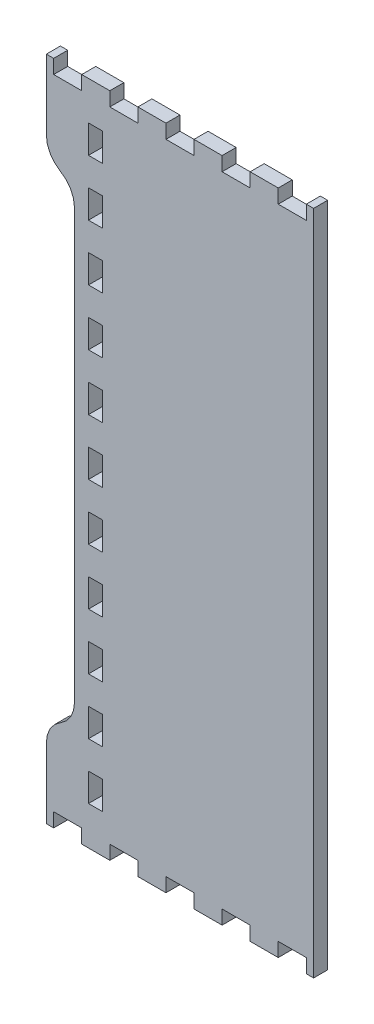
SolidWorks part; units mm, degrees
ref_plane "Front Plane" through (0, 0, 0) normal (0, 0, 1) x (1, 0, 0)
ref_plane "Top Plane" through (0, 0, 0) normal (0, 1, 0) x (1, 0, 0)
ref_plane "Right Plane" through (0, 0, 0) normal (1, 0, 0) x (0, 0, -1)
sketch "Model" plane through (0, 0, 0) normal (0, 0, 1) x (1, 0, 0)
  line L558 (863.264, 22.8602) -> (866.2368, 22.8602)
  line L559 (866.2368, 22.8602) -> (866.2368, 28.5752)
  line L560 (866.2368, 28.5752) -> (877.6675, 28.5752)
  line L561 (877.6675, 28.5752) -> (877.6675, 22.8602)
  line L562 (877.6675, 22.8602) -> (889.0983, 22.8602)
  line L563 (889.0983, 22.8602) -> (889.0983, 28.5752)
  line L564 (889.0983, 28.5752) -> (900.529, 28.5752)
  line L565 (900.529, 28.5752) -> (900.529, 22.8602)
  line L566 (900.529, 22.8602) -> (911.9562, 22.8602)
  line L567 (911.9562, 22.8602) -> (911.9562, 28.5752)
  line L568 (911.9562, 28.5752) -> (923.3869, 28.5752)
  line L569 (923.3869, 28.5752) -> (923.3869, 22.8602)
  line L570 (923.3869, 22.8602) -> (934.8176, 22.8602)
  line L571 (934.8176, 22.8602) -> (934.8176, 28.5752)
  line L572 (934.8176, 28.5752) -> (946.2483, 28.5752)
  line L573 (946.2483, 28.5752) -> (946.2483, 22.8602)
  line L574 (946.2483, 22.8602) -> (957.679, 22.8602)
  line L575 (957.679, 22.8602) -> (957.679, 28.5752)
  line L576 (957.679, 28.5752) -> (969.1062, 28.5752)
  line L577 (969.1062, 28.5752) -> (969.1062, 22.8602)
  line L578 (969.1062, 22.8602) -> (972.0826, 22.8602)
  line L579 (972.0826, 22.8602) -> (972.0826, 28.5752)
  line L580 (972.0826, 28.5752) -> (972.0826, 288.5754)
  line L581 (972.0826, 288.5754) -> (972.0826, 294.2904)
  line L582 (972.0826, 294.2904) -> (969.1062, 294.2904)
  line L583 (969.1062, 294.2904) -> (969.1062, 288.5754)
  line L584 (969.1062, 288.5754) -> (957.679, 288.5754)
  line L585 (957.679, 288.5754) -> (957.679, 294.2904)
  line L586 (957.679, 294.2904) -> (946.2483, 294.2904)
  line L587 (946.2483, 294.2904) -> (946.2483, 288.5754)
  line L588 (946.2483, 288.5754) -> (934.8176, 288.5754)
  line L589 (934.8176, 288.5754) -> (934.8176, 294.2904)
  line L590 (934.8176, 294.2904) -> (923.3869, 294.2904)
  line L591 (923.3869, 294.2904) -> (923.3869, 288.5754)
  line L592 (923.3869, 288.5754) -> (911.9562, 288.5754)
  line L593 (911.9562, 288.5754) -> (911.9562, 294.2904)
  line L594 (911.9562, 294.2904) -> (900.529, 294.2904)
  line L595 (900.529, 294.2904) -> (900.529, 288.5754)
  line L596 (900.529, 288.5754) -> (889.0983, 288.5754)
  line L597 (889.0983, 288.5754) -> (889.0983, 294.2904)
  line L598 (889.0983, 294.2904) -> (877.6675, 294.2904)
  line L599 (877.6675, 294.2904) -> (877.6675, 288.5754)
  line L600 (877.6675, 288.5754) -> (866.2368, 288.5754)
  line L601 (866.2368, 288.5754) -> (866.2368, 294.2904)
  line L602 (866.2368, 294.2904) -> (863.264, 294.2904)
  line L603 (863.264, 294.2904) -> (863.264, 288.5754)
  line L604 (863.264, 288.5754) -> (863.264, 265.7154)
  line L605 (863.264, 265.7154) -> (863.6533, 262.7573)
  line L606 (863.6533, 262.7573) -> (864.7947, 260.0004)
  line L607 (864.7947, 260.0004) -> (866.6102, 257.6331)
  line L608 (866.6102, 257.6331) -> (868.9758, 255.8164)
  line L609 (868.9758, 255.8164) -> (871.3445, 254.0001)
  line L610 (871.3445, 254.0001) -> (873.1604, 251.6332)
  line L611 (873.1604, 251.6332) -> (874.3036, 248.8763)
  line L612 (874.3036, 248.8763) -> (874.6947, 245.9182)
  line L613 (874.6947, 245.9182) -> (874.6947, 71.2322)
  line L614 (874.6947, 71.2322) -> (874.3023, 68.2743)
  line L615 (874.3023, 68.2743) -> (873.1604, 65.5172)
  line L616 (873.1604, 65.5172) -> (871.3445, 63.1505)
  line L617 (871.3445, 63.1505) -> (868.9758, 61.3344)
  line L618 (868.9758, 61.3344) -> (866.6102, 59.5176)
  line L619 (866.6102, 59.5176) -> (864.7947, 57.1504)
  line L620 (864.7947, 57.1504) -> (863.6533, 54.3934)
  line L621 (863.6533, 54.3934) -> (863.264, 51.4354)
  line L622 (863.264, 51.4354) -> (863.264, 28.5752)
  line L623 (863.264, 28.5752) -> (863.264, 22.8602)
  line L624 (880.4101, 272.8754) -> (880.4101, 278.5904)
  line L625 (880.4101, 278.5904) -> (886.1219, 278.5904)
  line L626 (886.1219, 278.5904) -> (886.1219, 267.1603)
  line L627 (886.1219, 267.1603) -> (880.4101, 267.1603)
  line L628 (880.4101, 267.1603) -> (880.4101, 272.8754)
  line L629 (880.4101, 250.0153) -> (880.4101, 255.7303)
  line L630 (880.4101, 255.7303) -> (886.1219, 255.7303)
  line L631 (886.1219, 255.7303) -> (886.1219, 244.3003)
  line L632 (886.1219, 244.3003) -> (880.4101, 244.3003)
  line L633 (880.4101, 244.3003) -> (880.4101, 250.0153)
  line L634 (880.4101, 227.1553) -> (880.4101, 232.8703)
  line L635 (880.4101, 232.8703) -> (886.1219, 232.8703)
  line L636 (886.1219, 232.8703) -> (886.1219, 221.4403)
  line L637 (886.1219, 221.4403) -> (880.4101, 221.4403)
  line L638 (880.4101, 221.4403) -> (880.4101, 227.1553)
  line L639 (880.4101, 204.2953) -> (880.4101, 210.0103)
  line L640 (880.4101, 210.0103) -> (886.1219, 210.0103)
  line L641 (886.1219, 210.0103) -> (886.1219, 198.5803)
  line L642 (886.1219, 198.5803) -> (880.4101, 198.5803)
  line L643 (880.4101, 198.5803) -> (880.4101, 204.2953)
  line L644 (880.4101, 181.4352) -> (880.4101, 187.1503)
  line L645 (880.4101, 187.1503) -> (886.1219, 187.1503)
  line L646 (886.1219, 187.1503) -> (886.1219, 175.7202)
  line L647 (886.1219, 175.7202) -> (880.4101, 175.7202)
  line L648 (880.4101, 175.7202) -> (880.4101, 181.4352)
  line L649 (880.4101, 158.5752) -> (880.4101, 164.2902)
  line L650 (880.4101, 164.2902) -> (886.1219, 164.2902)
  line L651 (886.1219, 164.2902) -> (886.1219, 152.8602)
  line L652 (886.1219, 152.8602) -> (880.4101, 152.8602)
  line L653 (880.4101, 152.8602) -> (880.4101, 158.5752)
  line L654 (880.4101, 135.7152) -> (880.4101, 141.4302)
  line L655 (880.4101, 141.4302) -> (886.1219, 141.4302)
  line L656 (886.1219, 141.4302) -> (886.1219, 130.0002)
  line L657 (886.1219, 130.0002) -> (880.4101, 130.0002)
  line L658 (880.4101, 130.0002) -> (880.4101, 135.7152)
  line L659 (880.4101, 112.8552) -> (880.4101, 118.5702)
  line L660 (880.4101, 118.5702) -> (886.1219, 118.5702)
  line L661 (886.1219, 118.5702) -> (886.1219, 107.1402)
  line L662 (886.1219, 107.1402) -> (880.4101, 107.1402)
  line L663 (880.4101, 107.1402) -> (880.4101, 112.8552)
  line L664 (880.4101, 89.9951) -> (880.4101, 95.7101)
  line L665 (880.4101, 95.7101) -> (886.1219, 95.7101)
  line L666 (886.1219, 95.7101) -> (886.1219, 84.2801)
  line L667 (886.1219, 84.2801) -> (880.4101, 84.2801)
  line L668 (880.4101, 84.2801) -> (880.4101, 89.9951)
  line L669 (880.4101, 67.1351) -> (880.4101, 72.8501)
  line L670 (880.4101, 72.8501) -> (886.1219, 72.8501)
  line L671 (886.1219, 72.8501) -> (886.1219, 61.4201)
  line L672 (886.1219, 61.4201) -> (880.4101, 61.4201)
  line L673 (880.4101, 61.4201) -> (880.4101, 67.1351)
  line L674 (880.4101, 44.2751) -> (880.4101, 49.9901)
  line L675 (880.4101, 49.9901) -> (886.1219, 49.9901)
  line L676 (886.1219, 49.9901) -> (886.1219, 38.5601)
  line L677 (886.1219, 38.5601) -> (880.4101, 38.5601)
  line L678 (880.4101, 38.5601) -> (880.4101, 44.2751)
extrude "Boss-Extrude1" add sketch "Model" along normal blind 5.715
